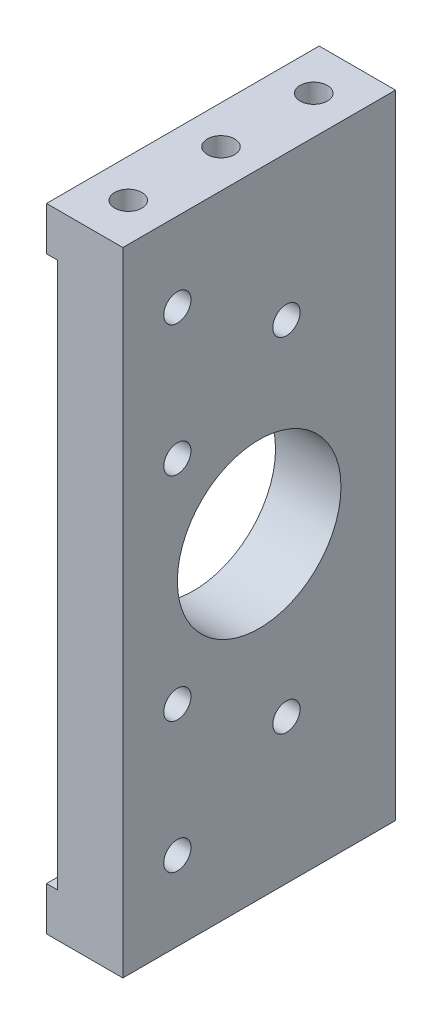
SolidWorks part; units mm, degrees
material "6061 合金"
ref_plane "前视基准面" through (0, 0, 0) normal (0, 0, 1) x (1, 0, 0)
ref_plane "上视基准面" through (0, 0, 0) normal (0, 1, 0) x (1, 0, 0)
ref_plane "右视基准面" through (0, 0, 0) normal (1, 0, 0) x (0, 0, -1)
sketch "草图1" plane through (0, 0, 0) normal (0, 0, 1) x (1, 0, 0)
  line L0 (0, 21.2234) -> (0, -15.6915) construction
  line L1 (-35.1073, 0) -> (42.2892, 0) construction
  line L2 (-81, -29) -> (86, -29)
  line L3 (-86, -29) -> (-86, -34)
  line L4 (-86, -34) -> (86, -34)
  line L5 (86, -29) -> (86, -34)
  line L8 (-86, -29) -> (-86, 29)
  line L9 (-86, 29) -> (-81, 29)
  line L10 (-81, -29) -> (-81, 29)
  dimension "D1" = 5
  dimension "D2" = 172
  dimension "D3" = 63
  dimension "D4" = 5
  dimension "D5" = 34
extrude "凸台-拉伸1" add sketch "草图1" along normal blind 25
sketch "草图2" plane through (0, 0, 25) normal (0, 0, 1) x (1, 0, 0)
  line L0 (0, 0) -> (-100.8625, 0) construction
  line L1 (-86, 29) -> (-86, -34) construction
  line L2 (-86, 25) -> (-85, 25)
  line L3 (-86, 25) -> (-86, -25)
  line L4 (-86, -25) -> (-85, -25)
  line L5 (-85, 25) -> (-85, -25)
  dimension "D1" = 1
  dimension "D2" = 50
extrude "切除-拉伸1" cut sketch "草图2" against normal through all
sketch "草图3" plane through (0, 0, 25) normal (0, 0, 1) x (1, 0, 0)
  line L0 (0, -34) -> (0, 0) construction
  line L1 (-86, -34) -> (86, -34) construction
  line L2 (86, -29) -> (-81, -29) construction
  line L3 (-26, -29) -> (26, -29)
  line L4 (-26, -29) -> (-26, -28)
  line L5 (-26, -28) -> (26, -28)
  line L6 (26, -29) -> (26, -28)
  dimension "D1" = 52
  dimension "D2" = 1
extrude "凸台-拉伸2" add sketch "草图3" against normal up to surface (25 mm away) up to face at (-50.4, -6.8, 0)
sketch "草图4" plane through (0, 0, 25) normal (0, 0, 1) x (1, 0, 0)
  line L1 (-81, -29) -> (-79, -29)
  line L2 (-81, -29) -> (-81, -28)
  line L3 (-81, -28) -> (-79, -28)
  line L4 (-79, -29) -> (-79, -28)
  dimension "D1" = 2
  dimension "D2" = 1
extrude "凸台-拉伸3" add sketch "草图4" against normal up to surface (25 mm away) up to face at (-36, -13, 0)
sketch "草图5" plane through (0, 0, 25) normal (0, 0, 1) x (1, 0, 0)
  line L0 (86, -29) -> (26, -29) construction
  line L1 (79, -29) -> (77, -29)
  line L2 (79, -29) -> (79, -28)
  line L3 (79, -28) -> (77, -28)
  line L4 (77, -29) -> (77, -28)
  line L5 (86, -34) -> (86, -29) construction
  dimension "D1" = 1
  dimension "D2" = 2
  dimension "D3" = 7
extrude "凸台-拉伸4" add sketch "草图5" against normal up to surface (25 mm away) up to face at (-41.375, -14.875, 0)
sketch "草图6" plane through (0, 0, 25) normal (0, 0, 1) x (1, 0, 0)
  line L0 (0, 0) -> (0, -34) construction
  line L1 (-86, -34) -> (86, -34) construction
  line L3 (-26, -34) -> (-15, -34)
  line L4 (-26, -34) -> (-26, -33)
  line L5 (-26, -33) -> (-15, -33)
  line L6 (-15, -34) -> (-15, -33)
  dimension "D1" = 11
  dimension "D2" = 1
  dimension "D3" = 15
extrude "切除-拉伸2" cut sketch "草图6" against normal through all
mirror "镜向1" about plane through (0, 0, 0) normal (1, 0, 0) of "切除-拉伸2"
sketch "草图7" plane through (0, -34, 0) normal (0, -1, 0) x (1, 0, 0)
  line L0 (-15, 12.5) -> (15, 12.5) construction
  line L1 (-15, 0) -> (-15, 25) construction
  line L2 (15, 0) -> (15, 25) construction
  line L3 (0, 25) -> (0, 0) construction
  line L4 (-15, 25) -> (15, 25) construction
  circle A0 centre (0, 12.5) radius 8.5
  dimension "D1" = 17
extrude "切除-拉伸3" cut sketch "草图7" against normal through all
sketch "草图8" plane through (0, -28, 0) normal (0, 1, 0) x (1, 0, 0)
  circle A0 centre (0, -12.5) radius 9.5
  dimension "D1" = 19
extrude "切除-拉伸4" cut sketch "草图8" against normal blind 5
sketch "草图9" plane through (0, 0, 0) normal (0, 0, -1) x (-1, 0, 0)
  line L1 (81, 29) -> (79, 29)
  line L2 (81, 29) -> (81, 24)
  line L3 (81, 24) -> (79, 24)
  line L4 (79, 29) -> (79, 24)
  dimension "D1" = 5
  dimension "D2" = 2
extrude "凸台-拉伸5" add sketch "草图9" against normal up to surface (25 mm away) up to face at (-12.5, -22.1429, 25)
sketch "草图11" plane through (0, -34, 0) normal (0, -1, 0) x (1, 0, 0)
  line L0 (82.5, 25) -> (82.5, 0) construction
  line L1 (26, 25) -> (86, 25) construction
  line L2 (26, 0) -> (86, 0) construction
  line L3 (86, 25) -> (86, 0) construction
  line L4 (86, 12.5) -> (82.5, 12.5) construction
  point P10 (82.5, 21)
  point P11 (82.5, 4)
  point P13 (82.5, 12.5)
  dimension "D2" = 4
  dimension "D1" = 3.5
hole_wizard "孔1" positions "3D草图1" profile "草图12" legacy end condition up to next
sketch3d "3D草图1"
  point P0 (82.5, -34, 21)
  point P3 (82.5, -34, 12.5)
  point P6 (82.5, -34, 4)
sketch "草图12" plane through (82.5, -34, 21) normal (1, 0, 0) x (0, 0, -1)
  line L0 (0, 0) -> (0, 5)
  line L1 (0, 5) -> (1.7, 5)
  line L2 (1.7, 5) -> (1.7, 3)
  line L3 (1.7, 3) -> (3, 3)
  line L4 (3, 3) -> (3, 0)
  line L5 (3, 0) -> (0, 0)
  line L6 (0, 110) -> (0, -10) construction
  dimension "直径" = 3.4
  dimension "深度" = 5
  dimension "柱坑直径" = 6
  dimension "柱坑深度" = 3
sketch "草图13" plane through (0, 29, 0) normal (0, 1, 0) x (1, 0, 0)
  line L0 (-82.5, 0) -> (-82.5, -25) construction
  line L1 (-79, 0) -> (-86, 0) construction
  line L2 (-79, -25) -> (-86, -25) construction
  line L3 (-86, -12.5) -> (-79, -12.5) construction
  line L4 (-86, -25) -> (-86, 0) construction
  line L5 (-79, -25) -> (-79, 0) construction
  circle A0 centre (-82.5, -12.5) radius 1.5
  circle A1 centre (-82.5, -4) radius 1.5
  circle A2 centre (-82.5, -21) radius 1.5
  dimension "D1" = 3
  dimension "D2" = 4
sketch "草图14" plane through (0, -33, 0) normal (0, -1, 0) x (1, 0, 0)
  line L0 (0, 0) -> (0, 48.2604) construction
  line L1 (-26, 12.5) -> (26, 12.5) construction
  line L2 (-26, 0) -> (-26, 25) construction
  line L3 (26, 0) -> (26, 25) construction
  line L4 (-26, 0) -> (-26, 25) construction
  line L7 (20.5, 25) -> (20.5, 0) construction
  line L8 (15, 25) -> (26, 25) construction
  line L9 (15, 0) -> (26, 0) construction
  circle A0 centre (-23, 20) radius 1.5
  circle A1 centre (-23, 5) radius 1.5
  dimension "D1" = 3
  dimension "D2" = 15
  dimension "D3" = 3
extrude "切除-拉伸8" cut sketch "草图14" against normal up to next (5 mm away)
cosmetic thread "装饰螺纹线4" parameters "D2"=3.2
cosmetic thread "装饰螺纹线5" parameters "D2"=3.2
mirror "镜向2" about plane through (0, 0, 0) normal (1, 0, 0) of "切除-拉伸8"
cosmetic thread "装饰螺纹线6" parameters "D2"=3.2
cosmetic thread "装饰螺纹线7" parameters "D2"=3.2
sketch "草图22" plane through (-81, 0, 0) normal (1, 0, 0) x (0, 0, -1)
  line L4 (0, -28) -> (0, 24)
  line L5 (0, 24) -> (-25, 24)
  line L6 (-25, 24) -> (-25, -28)
  line L7 (-25, -28) -> (0, -28)
  line L8 (0, -28) -> (0, 24)
  line L9 (0, 24) -> (-25, 24)
  line L10 (-25, 24) -> (-25, -28)
  line L11 (-25, -28) -> (0, -28)
  dimension "D1" = 0
extrude "凸台-拉伸9" add sketch "草图22" along normal up to surface (2 mm away) up to face at (-79, 26.5, 12.5)
sketch "草图15" plane through (-85, 0, 0) normal (-1, 0, 0) x (0, 0, 1)
  circle A0 centre (20, 21.75) radius 1.25
  circle A1 centre (20, 9.75) radius 1.25
  circle A2 centre (10, 15.75) radius 1.25
  circle A3 centre (20, -9.75) radius 1.25
  circle A4 centre (20, -21.75) radius 1.25
  circle A5 centre (10, -15.75) radius 1.25
  dimension "D1" = 2.5
sketch "草图16" plane through (0, -34, 0) normal (0, -1, 0) x (1, 0, 0)
  line L1 (-73, 20) -> (-30, 20)
  line L2 (-78, 15) -> (-78, 10)
  line L3 (-73, 5) -> (-30, 5)
  line L4 (-25, 15) -> (-25, 10)
  line L5 (-86, 25) -> (-86, 0) construction
  line L6 (-15, 0) -> (-15, 25) construction
  line L7 (-86, 25) -> (-26, 25) construction
  line L8 (-86, 0) -> (-26, 0) construction
  arc A0 (-30, 5) -> (-25, 10) centre (-30, 10) ccw
  arc A1 (-30, 20) -> (-25, 15) centre (-30, 15) cw
  arc A2 (-78, 10) -> (-73, 5) centre (-73, 10) ccw
  arc A3 (-73, 20) -> (-78, 15) centre (-73, 15) ccw
  dimension "D5" = 5
  dimension "D1" = 8
  dimension "D2" = 10
  dimension "D3" = 5
  dimension "D4" = 5
extrude "切除-拉伸10" cut sketch "草图16" against normal up to next
mirror "镜向3" about plane through (0, 0, 0) normal (1, 0, 0) of "切除-拉伸10"
sketch "草图17" plane through (-85, 0, 0) normal (-1, 0, 0) x (0, 0, 1)
  line L0 (0, -25) -> (0, 25) construction
  circle A0 centre (12.5, 0) radius 7.5
  dimension "D1" = 12.5
  dimension "D2" = 15
extrude "切除-拉伸11" cut sketch "草图17" against normal up to next
sketch "草图18" plane through (0, 0, 25) normal (0, 0, 1) x (1, 0, 0)
  line L0 (-79, -29) -> (-86, -29)
  line L1 (-86, -25) -> (-86, -34) construction
  line L2 (-86, -29) -> (-86, -34)
  line L3 (-86, -34) -> (86, -34)
  line L4 (86, -34) -> (86, -25.7591)
  line L5 (86, -25.7591) -> (-79, -25.7591)
  line L6 (-79, -25.7591) -> (-79, -29)
extrude "切除-拉伸12" cut sketch "草图18" against normal blind 60
hole_wizard "M3 螺纹孔1" positions "3D草图2" profile "草图23" tap size "M3" standard "GB"
sketch3d "3D草图2"
  point P0 (-85, 21.75, 20)
  point P3 (-85, 9.75, 20)
  point P6 (-85, 15.75, 10)
  point P9 (-85, -9.75, 20)
  point P12 (-85, -21.75, 20)
  point P15 (-85, -15.75, 10)
sketch "草图23" plane through (-85, 21.75, 20) normal (0, 1, 0) x (0, 0, 1)
  line L0 (0, 0) -> (0, 9.2511)
  line L1 (0, 9.2511) -> (1.25, 8.5)
  line L2 (1.25, 8.5) -> (1.25, 0)
  line L5 (1.25, 0) -> (0, 0)
  line L10 (0, 9.2511) -> (-1.25, 8.5) construction
  line L11 (0, -6.35) -> (0, 107.95) construction
  dimension "螺纹孔钻头直径" = 2.5
  dimension "螺纹孔钻头深度" = 8.5
  dimension "导头角度" = 118
cosmetic thread "孔螺蚊线1" parameters "D1"=6, "D2"=3
cosmetic thread "孔螺蚊线2" parameters "D1"=6, "D2"=3
cosmetic thread "孔螺蚊线3" parameters "D1"=6, "D2"=3
cosmetic thread "孔螺蚊线4" parameters "D1"=6, "D2"=3
cosmetic thread "孔螺蚊线5" parameters "D1"=6, "D2"=3
cosmetic thread "孔螺蚊线6" parameters "D1"=6, "D2"=3
hole_wizard "M3 螺纹孔2" positions "3D草图3" profile "草图24" tap size "M3" standard "GB"
sketch3d "3D草图3"
  point P0 (-82.5, 29, 21)
  point P3 (-82.5, 29, 12.5)
  point P6 (-82.5, 29, 4)
sketch "草图24" plane through (-82.5, 29, 21) normal (1, 0, 0) x (0, 0, 1)
  line L0 (0, 0) -> (0, 5.7511)
  line L1 (0, 5.7511) -> (1.25, 5)
  line L2 (1.25, 5) -> (1.25, 0)
  line L5 (1.25, 0) -> (0, 0)
  line L10 (0, 5.7511) -> (-1.25, 5) construction
  line L11 (0, -6.35) -> (0, 107.95) construction
  dimension "螺纹孔钻头直径" = 2.5
  dimension "螺纹孔钻头深度" = 5
  dimension "导头角度" = 118
cosmetic thread "孔螺蚊线7" parameters "D1"=5, "D2"=3
cosmetic thread "孔螺蚊线8" parameters "D1"=5, "D2"=3
cosmetic thread "孔螺蚊线9" parameters "D1"=5, "D2"=3
ref_plane "基准面1" through (0, 0, 0) normal (0, 1, 0) x (1, 0, 0)
mirror "镜向4" about plane through (0, 0, 0) normal (0, 1, 0) of "M3 螺纹孔2"
